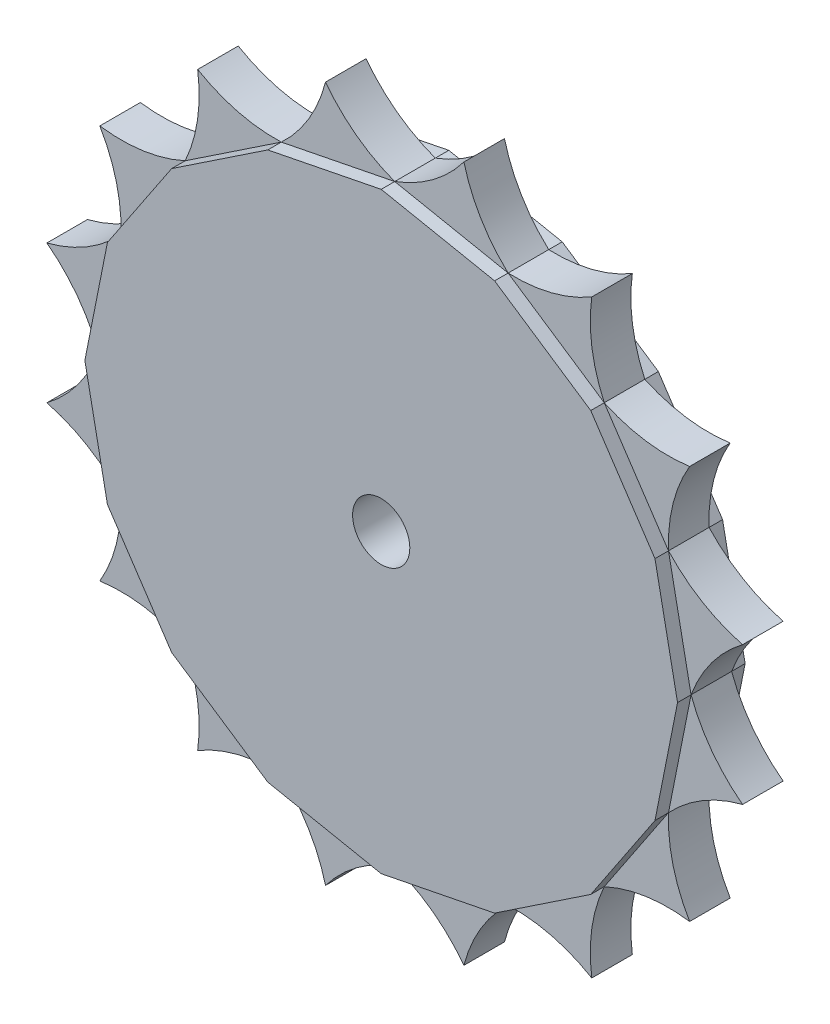
SolidWorks part; units mm, degrees
ref_plane "Ön Düzlem" through (0, 0, 0) normal (0, 0, 1) x (1, 0, 0)
ref_plane "Üst Düzlem" through (0, 0, 0) normal (0, 1, 0) x (1, 0, 0)
ref_plane "Sağ Düzlem" through (0, 0, 0) normal (1, 0, 0) x (0, 0, -1)
sketch "Çizim1" plane through (0, 0, 0) normal (0, 0, 1) x (1, 0, 0)
  line L0 (22.431, 0) -> (-22.431, 0) construction
  line L1 (20.0825, 0) -> (18.4138, 8.3889)
  line L2 (18.4138, 8.3889) -> (13.6619, 15.5006)
  line L3 (13.6619, 15.5006) -> (6.5502, 20.2526)
  line L4 (6.5502, 20.2526) -> (-1.8387, 21.9212)
  line L5 (-1.8387, 21.9212) -> (-10.2276, 20.2526)
  line L6 (-10.2276, 20.2526) -> (-17.3393, 15.5006)
  line L7 (-17.3393, 15.5006) -> (-22.0913, 8.3889)
  line L8 (-22.0913, 8.3889) -> (-23.7599, 0)
  line L9 (-23.7599, 0) -> (-22.0913, -8.3889)
  line L10 (-22.0913, -8.3889) -> (-17.3393, -15.5006)
  line L11 (-17.3393, -15.5006) -> (-10.2276, -20.2526)
  line L12 (-10.2276, -20.2526) -> (-1.8387, -21.9212)
  line L13 (-1.8387, -21.9212) -> (6.5502, -20.2526)
  line L14 (6.5502, -20.2526) -> (13.6619, -15.5006)
  line L15 (13.6619, -15.5006) -> (18.4138, -8.3889)
  line L16 (18.4138, -8.3889) -> (20.0825, 0)
  circle A0 centre (-1.8387, 0) radius 21.5 construction
extrude "Yükseklik-Ekstrüzyon1" add sketch "Çizim1" along normal mid plane 5
sketch "Çizim3" plane through (0, 0, -2.5) normal (0, 0, -1) x (-1, 0, 0)
  line L0 (-13.6619, 15.5006) -> (17.3393, -15.5006) construction
  circle A0 centre (1.8387, 0) radius 2.1165
extrude "Kes-Ekstrüzyon2" cut sketch "Çizim3" against normal blind 31
sketch "Çizim6" plane through (0, 0, 0) normal (0, 0, 1) x (1, 0, 0)
  line L0 (-10.2276, 20.2526) -> (-1.8387, 21.9212)
  line L1 (-1.8387, 21.9212) -> (6.5502, 20.2526)
  line L2 (6.5502, 20.2526) -> (13.6619, 15.5006)
  line L3 (13.6619, 15.5006) -> (18.4138, 8.3889)
  line L4 (18.4138, 8.3889) -> (20.0825, 0)
  line L5 (20.0825, 0) -> (18.4138, -8.3889)
  line L6 (18.4138, -8.3889) -> (13.6619, -15.5006)
  line L7 (13.6619, -15.5006) -> (6.5502, -20.2526)
  line L8 (6.5502, -20.2526) -> (-1.8387, -21.9212)
  line L9 (-1.8387, -21.9212) -> (-10.2276, -20.2526)
  line L10 (-10.2276, -20.2526) -> (-17.3393, -15.5006)
  line L11 (-17.3393, -15.5006) -> (-22.0913, -8.3889)
  line L12 (-22.0913, -8.3889) -> (-23.7599, 0)
  line L13 (-23.7599, 0) -> (-22.0913, 8.3889)
  line L14 (-22.0913, 8.3889) -> (-17.3393, 15.5006)
  line L15 (-17.3393, 15.5006) -> (-10.2276, 20.2526)
  arc A0 (-6.9573, 25.7329) -> (-10.2276, 20.2526) centre (-17.9144, 28.5554) cw
  arc A1 (-6.9573, 25.7329) -> (-1.8387, 21.9212) centre (2.0856, 32.5337) ccw
  arc A2 (3.2799, 25.7329) -> (-1.8387, 21.9212) centre (-5.763, 32.5337) cw
  arc A3 (3.2799, 25.7329) -> (6.5502, 20.2526) centre (14.237, 28.5554) ccw
  arc A4 (12.7378, 21.8153) -> (6.5502, 20.2526) centre (6.9858, 31.559) cw
  arc A5 (12.7378, 21.8153) -> (13.6619, 15.5006) centre (23.941, 20.2299) ccw
  arc A6 (19.9766, 14.5765) -> (13.6619, 15.5006) centre (18.3912, 25.7797) cw
  arc A7 (19.9766, 14.5765) -> (18.4138, 8.3889) centre (29.7202, 8.8245) ccw
  arc A8 (23.8942, 5.1186) -> (18.4138, 8.3889) centre (26.7167, 16.0757) cw
  arc A9 (23.8942, 5.1186) -> (20.0825, 0) centre (30.695, -3.9243) ccw
  arc A10 (23.8942, -5.1186) -> (20.0825, 0) centre (30.695, 3.9243) cw
  arc A11 (23.8942, -5.1186) -> (18.4138, -8.3889) centre (26.7167, -16.0757) ccw
  arc A12 (19.9766, -14.5765) -> (18.4138, -8.3889) centre (29.7202, -8.8245) cw
  arc A13 (19.9766, -14.5765) -> (13.6619, -15.5006) centre (18.3912, -25.7797) ccw
  arc A14 (12.7378, -21.8153) -> (13.6619, -15.5006) centre (23.941, -20.2299) cw
  arc A15 (12.7378, -21.8153) -> (6.5502, -20.2526) centre (6.9858, -31.559) ccw
  arc A16 (3.2799, -25.7329) -> (6.5502, -20.2526) centre (14.237, -28.5554) cw
  arc A17 (3.2799, -25.7329) -> (-1.8387, -21.9212) centre (-5.763, -32.5337) ccw
  arc A18 (-6.9573, -25.7329) -> (-1.8387, -21.9212) centre (2.0856, -32.5337) cw
  arc A19 (-6.9573, -25.7329) -> (-10.2276, -20.2526) centre (-17.9144, -28.5554) ccw
  arc A20 (-16.4152, -21.8153) -> (-10.2276, -20.2526) centre (-10.6632, -31.559) cw
  arc A21 (-16.4152, -21.8153) -> (-17.3393, -15.5006) centre (-27.6184, -20.2299) ccw
  arc A22 (-23.654, -14.5765) -> (-17.3393, -15.5006) centre (-22.0686, -25.7797) cw
  arc A23 (-23.654, -14.5765) -> (-22.0913, -8.3889) centre (-33.3977, -8.8245) ccw
  arc A24 (-27.5716, -5.1186) -> (-22.0913, -8.3889) centre (-30.3941, -16.0757) cw
  arc A25 (-27.5716, -5.1186) -> (-23.7599, 0) centre (-34.3724, 3.9243) ccw
  arc A26 (-27.5716, 5.1186) -> (-23.7599, 0) centre (-34.3724, -3.9243) cw
  arc A27 (-27.5716, 5.1186) -> (-22.0913, 8.3889) centre (-30.3941, 16.0757) ccw
  arc A28 (-23.654, 14.5765) -> (-22.0913, 8.3889) centre (-33.3977, 8.8245) cw
  arc A29 (-23.654, 14.5765) -> (-17.3393, 15.5006) centre (-22.0686, 25.7797) ccw
  arc A30 (-16.4152, 21.8153) -> (-17.3393, 15.5006) centre (-27.6184, 20.2299) cw
  arc A31 (-16.4152, 21.8153) -> (-10.2276, 20.2526) centre (-10.6632, 31.559) ccw
  point P84 (-1.8387, 0)
  dimension "D1" = 16
extrude "Yükseklik-Ekstrüzyon3" add sketch "Çizim6" along normal mid plane 3 contours A1 A0 L0 | A3 A2 L1 | A5 A4 L2 | A7 A6 L3 | A9 A8 L4 | A11 A10 L5 | A13 A12 L6 | A15 A14 L7 | A17 A16 L8 | A19 A18 L9 | A21 A20 L10 | A23 A22 L11 | A25 A24 L12 | A27 A26 L13 | A29 A28 L14 | A31 A30 L15
ref_plane "Plane1" through (0, 0, 2.5) normal (0, 0, 1) x (1, 0, 0)
sketch "Sketch1" plane through (0, 0, 2.5) normal (0, 0, 1) x (1, 0, 0)
  circle A0 centre (-1.8387, 0) radius 20.3792
